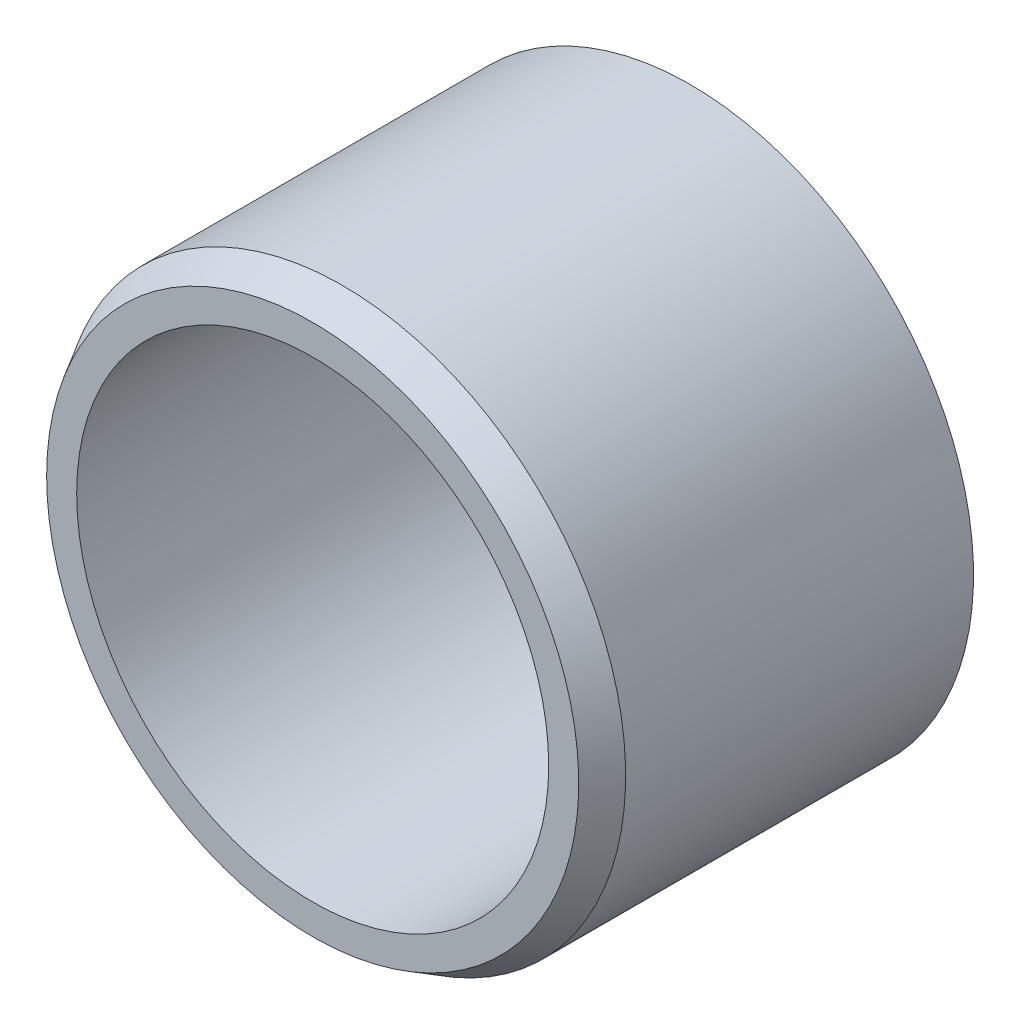
SolidWorks part; units mm, degrees
ref_plane "Front Plane" through (0, 0, 0) normal (0, 0, 1) x (1, 0, 0)
ref_plane "Top Plane" through (0, 0, 0) normal (0, 1, 0) x (1, 0, 0)
ref_plane "Right Plane" through (0, 0, 0) normal (1, 0, 0) x (0, 0, -1)
ref_plane "Plane1" through (0, 0, 0) normal (0, -1, 0) x (1, 0, 0)
sketch "Sketch1" plane through (0, 0, 0) normal (0, -1, 0) x (1, 0, 0)
  line L0 (4.4738, 6.35) -> (3.9688, 6.35)
  line L1 (3.9688, 6.35) -> (3.9688, 0.5)
  line L2 (3.9688, 0.5) -> (4.2574, 0)
  line L3 (4.2574, 0) -> (4.7625, 0)
  line L4 (4.7625, 0) -> (4.7625, 5.85)
  line L5 (4.7625, 5.85) -> (4.4738, 6.35)
  line L6 (0, 6.35) -> (0, 0) construction
revolve "Revolve1" add sketch "Sketch1" angle 360 about L6
